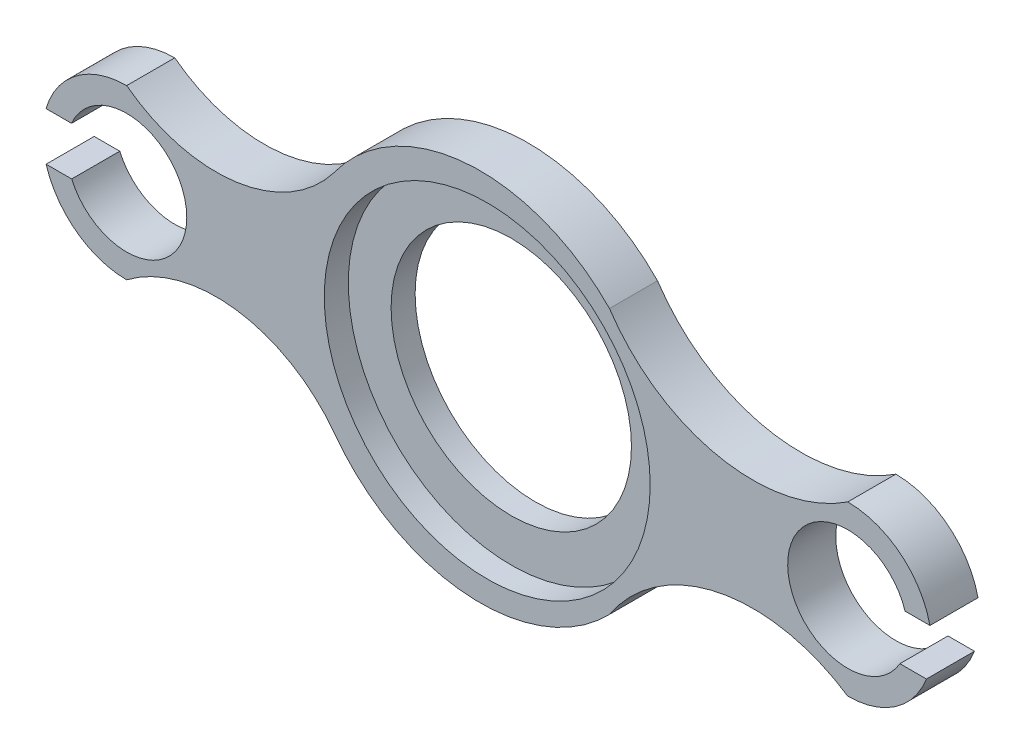
SolidWorks part; units mm, degrees
ref_plane "Front Plane" through (0, 0, 0) normal (0, 0, 1) x (1, 0, 0)
ref_plane "Top Plane" through (0, 0, 0) normal (0, 1, 0) x (1, 0, 0)
ref_plane "Right Plane" through (0, 0, 0) normal (1, 0, 0) x (0, 0, -1)
sketch "Sketch1" plane through (0, 0, 0) normal (0, 0, 1) x (1, 0, 0)
  circle A0 centre (0, 0) radius 50
  circle A1 centre (0, 0) radius 67.8
  dimension "D1" = 135.6
  dimension "D2" = 100
extrude "Boss-Extrude1" add sketch "Sketch1" along normal blind 10
sketch "Sketch2" plane through (0, 0, 0) normal (0, 0, 1) x (1, 0, 0)
  line L0 (-150, 0) -> (150, 0)
  line L1 (-175, 12.6864) -> (-175, -12.6864)
  line L2 (0, 67.8) -> (0, 77.8) construction
  line L3 (150, 25) -> (150, 35) construction
  line L4 (-150, 25) -> (-150, 35) construction
  circle A0 centre (-150, 0) radius 25
  circle A1 centre (150, 0) radius 25
  arc A2 (-63.7727, 46.7465) -> (50.8444, 55.1138) centre (-2.9548, 2.8582) cw
  circle A3 centre (0, 0) radius 67.8 construction
  arc A4 (-63.7727, -46.7465) -> (50.8444, -55.1138) centre (-2.9548, -2.8582) ccw
  arc A5 (-63.7727, 46.7465) -> (-150, 35) centre (-112.7596, 83.9869) cw
  arc A6 (-63.7727, -46.7465) -> (-150, -35) centre (-112.7596, -83.9869) ccw
  arc A7 (50.8444, 55.1138) -> (150, 35) centre (110.4791, 94.6347) ccw
  arc A8 (50.8444, -55.1138) -> (150, -35) centre (110.4791, -94.6347) cw
  arc A9 (-150, 35) -> (-150, -35) centre (-150, 0) ccw
  arc A10 (150, 35) -> (150, -35) centre (150, 0) cw
  point P5 (0, 0)
  point P11 (-175, 0)
  dimension "D2" = 50
  dimension "D3" = 50
  dimension "D4" = 75
  dimension "D5" = 10
  dimension "D6" = 10
  dimension "D7" = 10
  dimension "D1" = 300
extrude "Boss-Extrude2" add sketch "Sketch2" along normal blind 20
sketch "Sketch3" plane through (0, 0, 20) normal (0, 0, 1) x (1, 0, 0)
  circle A0 centre (0, 0) radius 67.8
  dimension "D1" = 135.6
extrude "Cut-Extrude1" cut sketch "Sketch3" against normal blind 10
sketch "Sketch4" plane through (0, 0, 10) normal (0, 0, 1) x (1, 0, 0)
  circle A0 centre (0, 0) radius 50
  dimension "D1" = 100
extrude "Cut-Extrude2" cut sketch "Sketch4" against normal through all
sketch "Sketch5" plane through (0, 0, 20) normal (0, 0, 1) x (1, 0, 0)
  line L1 (-187.9605, 9.9238) -> (-172.8795, 9.9238)
  line L2 (-187.9605, 9.9238) -> (-187.9605, -10.0762)
  line L3 (-187.9605, -10.0762) -> (-172.8795, -10.0762)
  line L4 (-172.8795, 9.9238) -> (-172.8795, -10.0762)
  line L5 (-187.9605, 9.9238) -> (-172.8795, -10.0762) construction
  line L6 (-187.9605, -10.0762) -> (-172.8795, 9.9238) construction
  circle A0 centre (-150, 0) radius 25 construction
  point P0 (-180.42, -0.0762)
  dimension "D1" = 20
extrude "Cut-Extrude3" cut sketch "Sketch5" against normal through all
sketch "Sketch6" plane through (0, 0, 20) normal (0, 0, 1) x (1, 0, 0)
  line L1 (169.6763, 7.5573) -> (189.3226, 7.5573)
  line L2 (169.6763, 7.5573) -> (169.6763, -12.4427)
  line L3 (169.6763, -12.4427) -> (189.3226, -12.4427)
  line L4 (189.3226, 7.5573) -> (189.3226, -12.4427)
  line L5 (169.6763, 7.5573) -> (189.3226, -12.4427) construction
  line L6 (169.6763, -12.4427) -> (189.3226, 7.5573) construction
  point P0 (179.4995, -2.4427)
  dimension "D1" = 20
extrude "Cut-Extrude4" cut sketch "Sketch6" against normal through all
